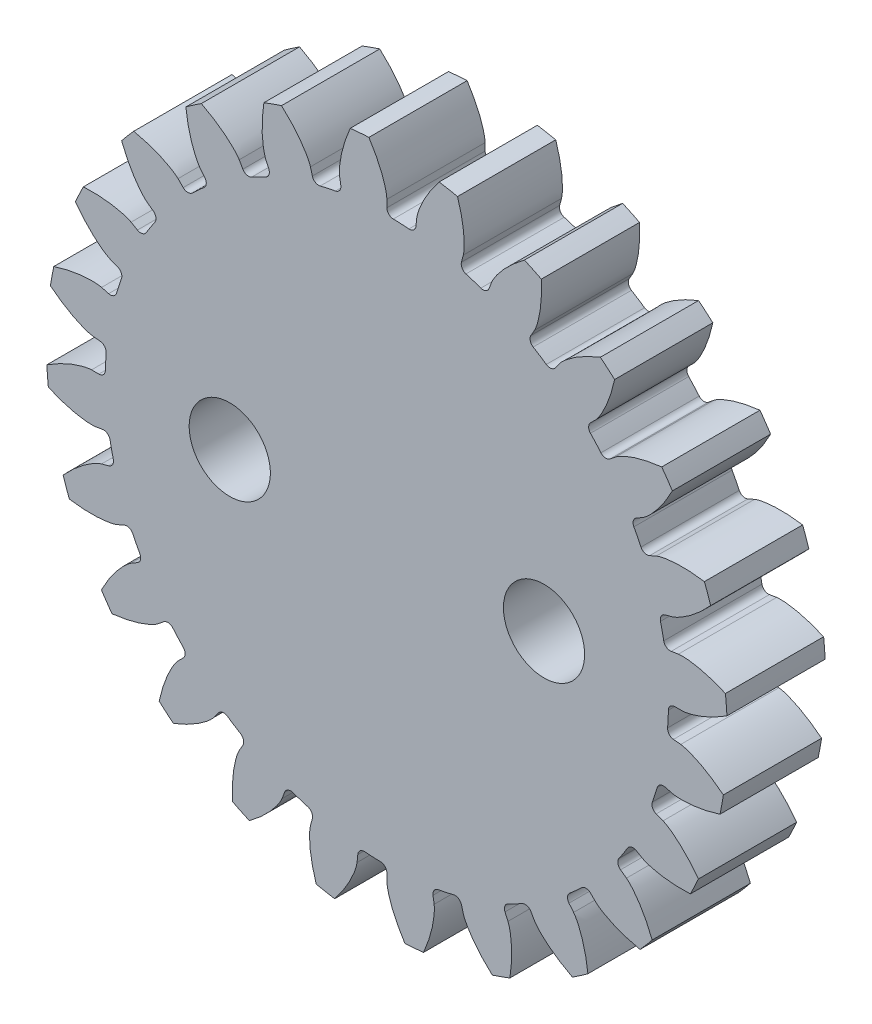
SolidWorks part; units mm, degrees
material "3.1325 (EN-AW 2017A)"
ref_plane "Front" through (0, 0, 0) normal (0, 0, 1) x (1, 0, 0)
ref_plane "Top" through (0, 0, 0) normal (0, 1, 0) x (1, 0, 0)
ref_plane "Right" through (0, 0, 0) normal (1, 0, 0) x (0, 0, -1)
sketch "ｽｹｯﾁ1" plane through (0, 0, 0) normal (0, 0, 1) x (1, 0, 0)
  line L0 (22.5526, 0) -> (0, 0) construction
  line L1 (22.5526, 0) -> (21.5, 0)
  line L2 (0, 0) -> (25.9668, -1.3136)
  circle A0 centre (0, 0) radius 22.5526 construction
  circle A1 centre (0, 0) radius 21.5 construction
  circle A2 centre (0, 0) radius 24 construction
  circle A3 centre (0, 0) radius 26
  arc A4 (21.5, 0) -> (21.4725, -1.0863) centre (0, 0) cw
  arc A5 (23.9973, 0.3577) -> (23.9693, -1.2126) centre (0, 0) cw
  spline S0 degree 4 poles (22.5526, 0) (22.5874, 0.0011) (22.6567, 0.0054) (22.8505, 0.0283) (23.2156, 0.0999) (23.764, 0.2576) (24.4933, 0.5458) (25.3932, 1.0005) (26.3919, 1.6314) (27.421, 2.4222) (28.4509, 3.3688) (29.4028, 4.3935) (30.2783, 5.4838) (31.1188, 6.6866) (32.0583, 8.2419) (33.024, 10.183) (33.9312, 12.5326) (34.6768, 15.2302) (35.1717, 17.9843) (35.4277, 20.7703) (35.4563, 23.5676) (35.2683, 26.3585) (34.9241, 28.7814) (34.5417, 30.6653) (34.2091, 32.0222) (33.9364, 33.0347) (33.6419, 34.0391) (33.318, 35.0387) (32.9699, 36.023) (32.6584, 36.8453) (32.4056, 37.4843) (32.1525, 38.0917) (31.9408, 38.5845) (31.6913, 39.1427) (31.5261, 39.5026) (31.2539, 40.0814) (31.0342, 40.5277) (30.7638, 41.0681) (30.5147, 41.5456) (30.242, 42.0581) (29.9755, 42.5406) (29.7632, 42.9175) (29.6249, 43.1564) (29.5531, 43.2804) knots 0 0 0 0 0 0.002802 0.005604 0.015718 0.02996 0.048734 0.068727 0.096889 0.125051 0.153212 0.181374 0.209535 0.237696 0.271429 0.327752 0.384075 0.440398 0.496721 0.553044 0.609367 0.66569 0.722013 0.750174 0.764255 0.778336 0.806497 0.834659 0.84874 0.86282 0.876901 0.890982 0.900036 0.909091 0.920455 0.931818 0.943182 0.954545 0.965909 0.977273 0.988636 1 1 1 1 1 construction
  spline S1 degree 4 poles (22.5526, 0) (22.5874, 0.0011) (22.6567, 0.0054) (22.8505, 0.0283) (23.2156, 0.0999) (23.764, 0.2576) (24.4933, 0.5458) (25.3932, 1.0005) (26.3919, 1.6314) (27.421, 2.4222) (28.4509, 3.3688) (29.4028, 4.3935) (30.2783, 5.4838) (31.1188, 6.6866) (32.0583, 8.2419) (33.024, 10.183) (33.9312, 12.5326) (34.6768, 15.2302) (35.1717, 17.9843) (35.4277, 20.7703) (35.4563, 23.5676) (35.2683, 26.3585) (34.9241, 28.7814) (34.5417, 30.6653) (34.2091, 32.0222) (33.9364, 33.0347) (33.6419, 34.0391) (33.318, 35.0387) (32.9699, 36.023) (32.6584, 36.8453) (32.4056, 37.4843) (32.1525, 38.0917) (31.9408, 38.5845) (31.7564, 38.9971) (31.6714, 39.1846) (31.6289, 39.2774) knots 0 0 0 0 0 0.002802 0.005604 0.015718 0.02996 0.048734 0.068727 0.096889 0.125051 0.153212 0.181374 0.209535 0.237696 0.271429 0.327752 0.384075 0.440398 0.496721 0.553044 0.609367 0.66569 0.722013 0.750174 0.764255 0.778336 0.806497 0.834659 0.84874 0.86282 0.876901 0.890982 0.900036 0.909091 0.909091 0.909091 0.909091 0.909091
  dimension "歯先円直径" = 52
  dimension "基礎円直径" = 45.1052
  dimension "基礎ピッチ円直径" = 48
  dimension "全歯たけ" = 4.5
  dimension "基準ピッチ/4" = 1.5708
sketch "ｽｹｯﾁ3" plane through (0, 0, 0) normal (0, 0, 1) x (1, 0, 0)
  circle A0 centre (0, 0) radius 26 construction
  circle A1 centre (0, 0) radius 26
extrude "ﾎﾞｽ - 押し出し2" add sketch "ｽｹｯﾁ3" along normal blind 7.5
sketch "ｽｹｯﾁ4" plane through (0, 0, 0) normal (0, 0, 1) x (1, 0, 0)
  line L0 (0, 0) -> (25.9668, -1.3136) construction
  line L1 (22.5526, 0) -> (21.5, 0) construction
  line L2 (21.4725, -1.0863) -> (25.9668, -1.3136)
  line L3 (22.5526, 0) -> (21.5, 0)
  arc A1 (21.4725, -1.0863) -> (21.5, 0) centre (0, 0) ccw construction
  circle A2 centre (0, 0) radius 26 construction
  arc A3 (21.4725, -1.0863) -> (21.5, 0) centre (0, 0) ccw
  arc A4 (25.9668, -1.3136) -> (25.9637, 1.373) centre (0, 0) ccw
  spline S1 degree 4 poles (15.1862, -999.773) (16.9514, 36.3954) (19.0933, 0.7282) (21.1742, -0.3006) (23.2156, 0.0999) (23.764, 0.2576) (24.4933, 0.5458) (25.3932, 1.0005) (26.3919, 1.6314) (27.421, 2.4222) (28.4509, 3.3688) (29.4028, 4.3935) (30.2783, 5.4838) (31.1188, 6.6866) (32.0583, 8.2419) (33.024, 10.183) (33.9312, 12.5326) (34.6768, 15.2302) (35.1717, 17.9843) (35.4277, 20.7703) (35.4563, 23.5676) (35.2683, 26.3585) (34.9241, 28.7814) (34.5417, 30.6653) (34.2091, 32.0222) (33.9364, 33.0347) (33.6419, 34.0391) (33.318, 35.0387) (32.9699, 36.023) (32.6584, 36.8453) (32.4056, 37.4843) (32.1525, 38.0917) (31.3467, 39.9673) (29.663, 43.4627) (43.99, 11.7586) (-384.9057, 948.343) knots -0.13757 -0.13757 -0.13757 -0.13757 -0.13757 0.002802 0.005604 0.015718 0.02996 0.048734 0.068727 0.096889 0.125051 0.153212 0.181374 0.209535 0.237696 0.271429 0.327752 0.384075 0.440398 0.496721 0.553044 0.609367 0.66569 0.722013 0.750174 0.764255 0.778336 0.806497 0.834659 0.84874 0.86282 0.876901 0.890982 0.900036 1.038953 1.038953 1.038953 1.038953 1.038953 only from (22.5526, 0) to (31.6289, 39.2774) construction
  spline S2 degree 4 poles (22.5526, 0) (22.5874, 0.0011) (22.6567, 0.0054) (22.8505, 0.0283) (23.2156, 0.0999) (23.764, 0.2576) (24.4933, 0.5458) (25.1482, 0.8767) (25.6277, 1.1589) (25.9005, 1.3322) (25.9637, 1.373) knots 0 0 0 0 0 0.002802 0.005604 0.015718 0.02996 0.048734 0.068727 0.074792 0.074792 0.074792 0.074792 0.074792
extrude "ｶｯﾄ - 押し出し2" cut sketch "ｽｹｯﾁ4" along normal through all
pattern_circular "円形ﾊﾟﾀｰﾝ1" count 24 over 360 about axis through (0, 0, 7.5) along (0, 0, -1) of "ｶｯﾄ - 押し出し2"
mirror "ﾐﾗｰ1" about plane through (21.4725, -1.0863, 7.5) normal (0.0505, 0.9987, 0) of "円形ﾊﾟﾀｰﾝ1", "ｶｯﾄ - 押し出し2"
sketch "ｽｹｯﾁ5" plane through (0, 0, 7.5) normal (0, 0, 1) x (1, 0, 0)
  circle A0 centre (0, 0) radius 5.1
  dimension "D1" = 10.2
extrude "ｶｯﾄ - 押し出し3" [suppressed] cut sketch "ｽｹｯﾁ5" against normal through all
fillet "ﾌｨﾚｯﾄ5" radius 0.5 48 edges at (19.6094, 8.8161, 3.75) (18.6195, 10.75, 3.75) (16.6594, 13.5909, 3.75) (15.2028, 15.2028, 3.75) (12.5742, 17.4396, 3.75) (10.75, 18.6195, 3.75) (7.632, 20.0998, 3.75) (5.5646, 20.7674, 3.75) (2.1697, 21.3902, 3.75) (0, 21.5, 3.75) (-3.4404, 21.223, 3.75) (-5.5646, 20.7674, 3.75) (-8.8161, 19.6094, 3.75) (-10.75, 18.6195, 3.75) (-13.5909, 16.6594, 3.75) (-15.2028, 15.2028, 3.75) (-17.4396, 12.5742, 3.75) (-18.6195, 10.75, 3.75) (-20.0998, 7.632, 3.75) (-20.7674, 5.5646, 3.75) (-21.3902, 2.1697, 3.75) (-21.5, 0, 3.75) (-21.223, -3.4404, 3.75) (-20.7674, -5.5646, 3.75) (-19.6094, -8.8161, 3.75) (-18.6195, -10.75, 3.75) (-16.6594, -13.5909, 3.75) (-15.2028, -15.2028, 3.75) (-12.5742, -17.4396, 3.75) (-10.75, -18.6195, 3.75) (-7.632, -20.0998, 3.75) (-5.5646, -20.7674, 3.75) (-2.1697, -21.3902, 3.75) (0, -21.5, 3.75) (3.4404, -21.223, 3.75) (5.5646, -20.7674, 3.75) (8.8161, -19.6094, 3.75) (10.75, -18.6195, 3.75) (13.5909, -16.6594, 3.75) (15.2028, -15.2028, 3.75) (17.4396, -12.5742, 3.75) (18.6195, -10.75, 3.75) (20.0998, -7.632, 3.75) (20.7674, -5.5646, 3.75) (21.3902, -2.1697, 3.75) (21.5, 0, 3.75) (21.223, 3.4404, 3.75) (20.7674, 5.5646, 3.75)
sketch "ｽｹｯﾁ10" plane through (0, 0, 0) normal (0, 0, -1) x (-1, 0, 0)
  line L0 (12, 0) -> (-12, 0) construction
  circle A0 centre (-12, 0) radius 3.1
  circle A1 centre (12, 0) radius 3.1
  point P4 (0, 0)
  dimension "D1" = 24
  dimension "D2" = 6.2
extrude "ｶｯﾄ - 押し出し4" cut sketch "ｽｹｯﾁ10" against normal through all
equation "\"モジュール\"= 2"
equation "\"歯数\"= 24"
equation "\"圧力角\"= 20"
equation "\"歯幅\"= 7.5"
equation "\"D1@ﾎﾞｽ - 押し出し2\"=\"歯幅\""
equation "\"D1@円形ﾊﾟﾀｰﾝ1\"=\"歯数\""
equation "\"歯先円直径@ｽｹｯﾁ1\"=(\"歯数\"+2)*(\"モジュール\")"
equation "\"基礎円直径@ｽｹｯﾁ1\"=\"歯数\"*\"モジュール\"*cos(\"圧力角\")"
equation "\"全歯たけ@ｽｹｯﾁ1\"= \"モジュール\" * 2.25"
equation "\"基礎ピッチ円直径@ｽｹｯﾁ1\"=\"歯数\"*\"モジュール\""
equation "\"基準ピッチ/4@ｽｹｯﾁ1\" = PI * \"モジュール\" / 4"
